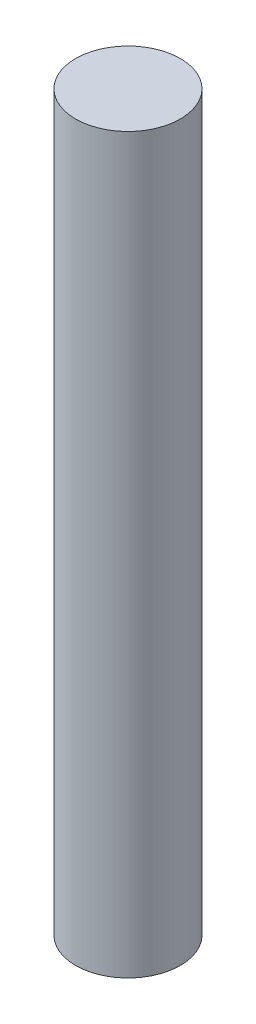
SolidWorks part; units mm, degrees
ref_plane "Front Plane" through (0, 0, 0) normal (0, 0, 1) x (1, 0, 0)
ref_plane "Top Plane" through (0, 0, 0) normal (0, 1, 0) x (1, 0, 0)
ref_plane "Right Plane" through (0, 0, 0) normal (1, 0, 0) x (0, 0, -1)
sketch "Sketch1" plane through (0, 0, 0) normal (0, 1, 0) x (1, 0, 0)
  circle A0 centre (0, 0) radius 1.5
  dimension "D1" = 3
extrude "Boss-Extrude1" add sketch "Sketch1" along normal blind 21
